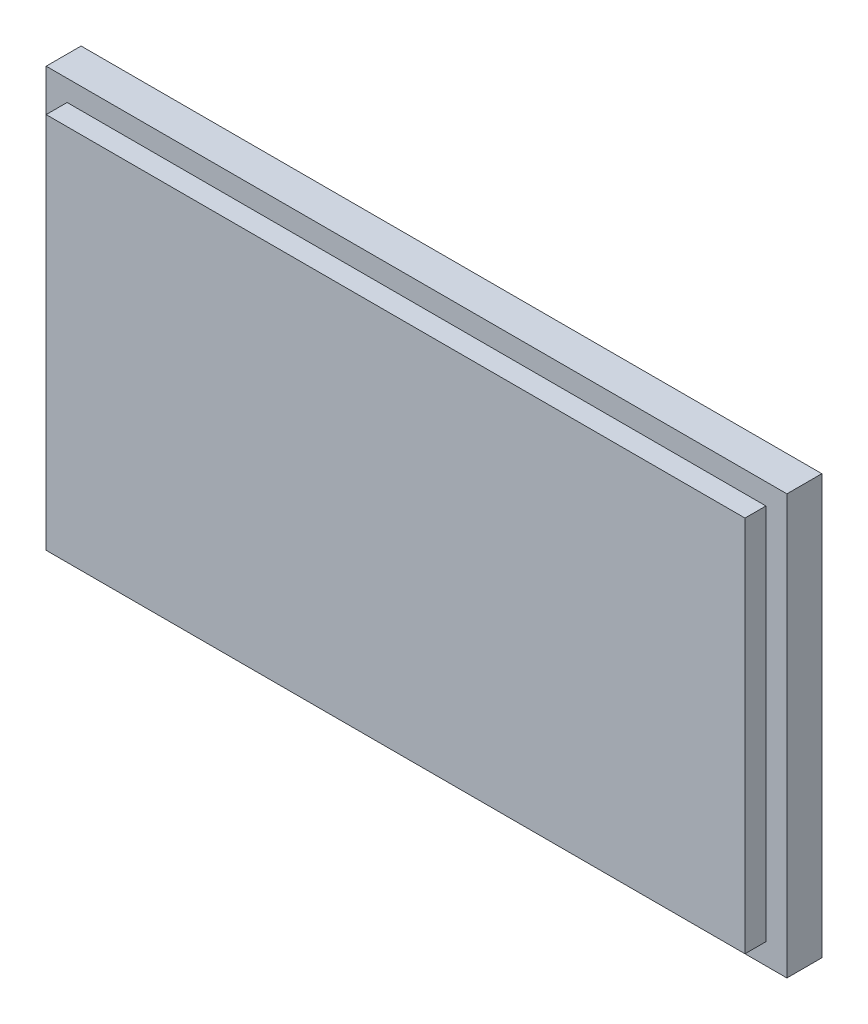
SolidWorks part; units mm, degrees
ref_plane "Front Plane" through (0, 0, 0) normal (0, 0, 1) x (1, 0, 0)
ref_plane "Top Plane" through (0, 0, 0) normal (0, 1, 0) x (1, 0, 0)
ref_plane "Right Plane" through (0, 0, 0) normal (1, 0, 0) x (0, 0, -1)
sketch "Sketch1" plane through (0, 0, 0) normal (0, 0, 1) x (1, 0, 0)
  line L1 (-26.5, 15) -> (26.5, 15)
  line L2 (-26.5, 15) -> (-26.5, -15)
  line L3 (-26.5, -15) -> (26.5, -15)
  line L4 (26.5, 15) -> (26.5, -15)
  line L5 (-26.5, 15) -> (26.5, -15) construction
  line L6 (-26.5, -15) -> (26.5, 15) construction
  point P0 (0, 0)
  dimension "D1" = 53
  dimension "D2" = 30
extrude "Boss-Extrude1" add sketch "Sketch1" along normal blind 4
sketch "Sketch2" plane through (0, 0, 4) normal (0, 0, 1) x (1, 0, 0)
  line L0 (26.5, 15) -> (-26.5, 15) construction
  line L1 (-25, 13.5) -> (25, 13.5)
  line L2 (-25, 13.5) -> (-25, -13.5)
  line L3 (-25, -13.5) -> (25, -13.5)
  line L4 (25, 13.5) -> (25, -13.5)
  line L5 (-25, 13.5) -> (25, -13.5) construction
  line L6 (-25, -13.5) -> (25, 13.5) construction
  line L7 (-26.5, 15) -> (-26.5, -15) construction
  point P0 (0, 0)
  dimension "D1" = 1.5
  dimension "D2" = 1.5
extrude "Cut-Extrude1" cut sketch "Sketch2" against normal blind 1.5 flip side to cut
